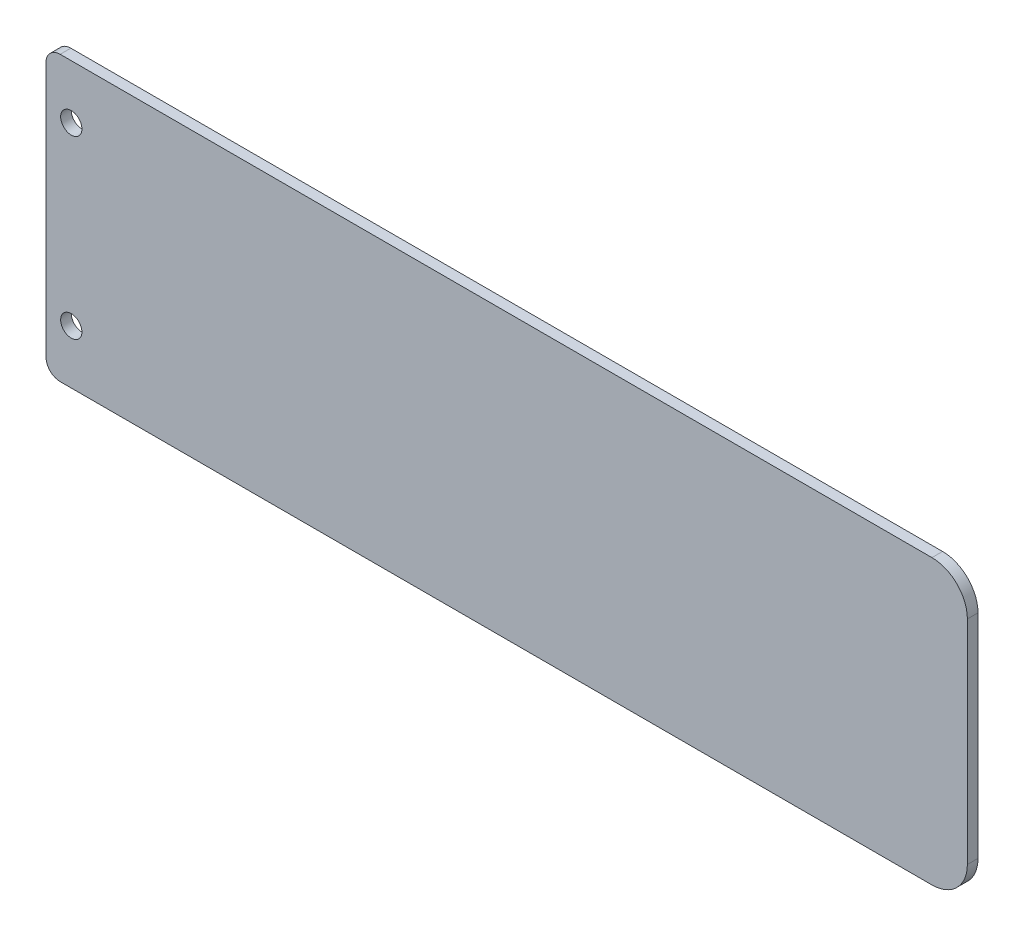
SolidWorks part; units mm, degrees
material "Verre"
ref_plane "Plan de face" through (0, 0, 0) normal (0, 0, 1) x (1, 0, 0)
ref_plane "Plan de dessus" through (0, 0, 0) normal (0, 1, 0) x (1, 0, 0)
ref_plane "Plan de droite" through (0, 0, 0) normal (1, 0, 0) x (0, 0, -1)
sketch "Esquisse1" plane through (0, 0, 0) normal (0, 0, 1) x (1, 0, 0)
  line L1 (0, 0) -> (260, 0)
  line L2 (0, 0) -> (0, 80)
  line L3 (0, 80) -> (260, 80)
  line L4 (260, 0) -> (260, 80)
  dimension "D1" = 260
  dimension "D2" = 80
extrude "Boss.-Extru.1" add sketch "Esquisse1" along normal blind 3
fillet "Congé1" radius 10 2 edges at (260, 0, 1.5) (260, 80, 1.5)
sketch "Esquisse2" plane through (0, 0, 3) normal (0, 0, 1) x (1, 0, 0)
  line L0 (0, 40) -> (260, 40) construction
  line L1 (0, 80) -> (0, 0) construction
  line L2 (260, 10) -> (260, 70) construction
sketch "Esquisse3" plane through (0, 0, 3) normal (0, 0, 1) x (1, 0, 0)
  circle A0 centre (7.1337, 64.8183) radius 3
  circle A1 centre (7.1337, 15.1939) radius 3
extrude "Enlèv. mat.-Extru.1" cut sketch "Esquisse3" against normal blind 10
fillet "Congé2" radius 4 2 edges at (0, 0, 1.5) (0, 80, 1.5)
